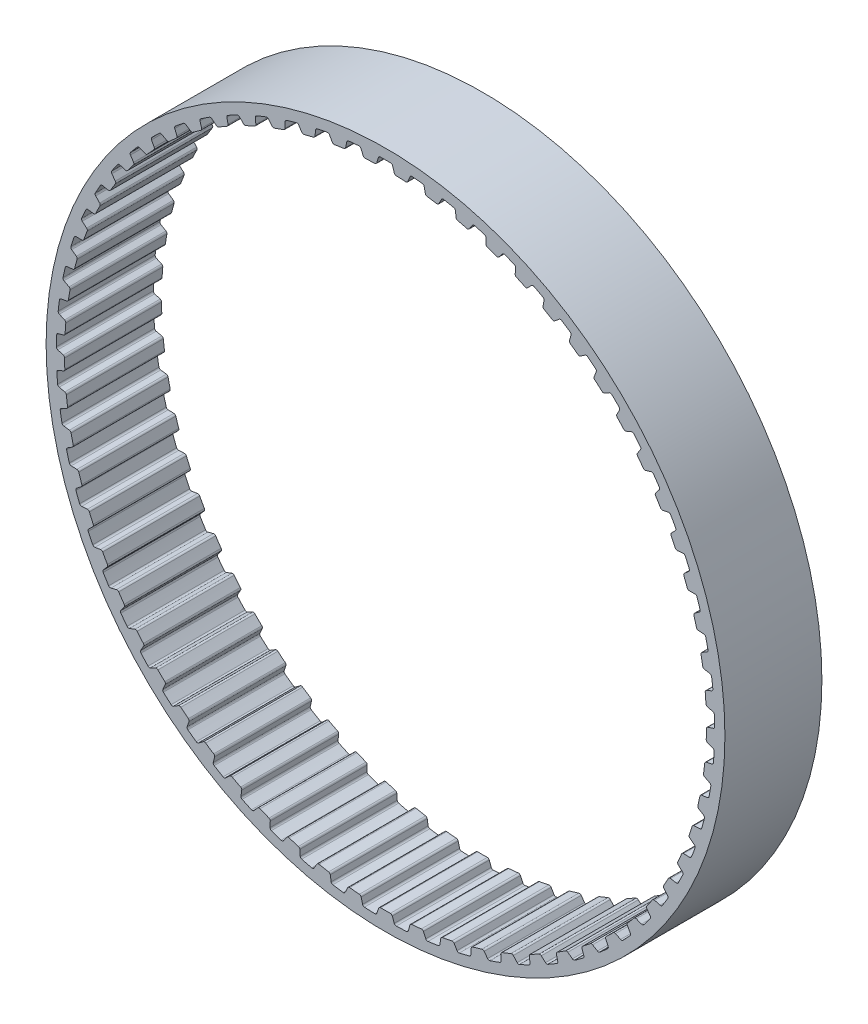
SolidWorks part; units mm, degrees
ref_plane "Front Plane" through (0, 0, 0) normal (0, 0, 1) x (1, 0, 0)
ref_plane "Top Plane" through (0, 0, 0) normal (0, 1, 0) x (1, 0, 0)
ref_plane "Right Plane" through (0, 0, 0) normal (1, 0, 0) x (0, 0, -1)
sketch "Sketch1" plane through (0, 0, 0) normal (0, 0, 1) x (1, 0, 0)
  line L0 (0, 0) -> (-0.9594, 19.8343) construction
  line L1 (0, 0) -> (0.9594, 19.8343) construction
  line L2 (0.9594, 19.8343) -> (-0.9594, 19.8343) construction
  line L3 (0.9594, 19.8343) -> (-0.9594, 19.8343) construction
  circle A0 centre (0, 0) radius 21.0005
  circle A1 centre (0, 0) radius 19.8575
  circle A2 centre (0, 0) radius 20.3655 construction
  dimension "OD" = 42.001
  dimension "Angle Distance" = 5.538
  dimension "hs" = 1.143
  dimension "ht" = 0.508
sketch "Sketch4" plane through (0, 0, 0) normal (0, 0, 1) x (1, 0, 0)
  circle A0 centre (0, 0) radius 19.8575 construction
  circle A1 centre (0, 0) radius 21.0005 construction
  circle A2 centre (0, 0) radius 19.8575
  circle A3 centre (0, 0) radius 21.0005
extrude "Boss-Extrude1" add sketch "Sketch4" along normal mid plane 6
sketch "Sketch2" plane through (0, 0, 0) normal (0, 0, 1) x (1, 0, 0)
  line L1 (0, 21.0005) -> (0, 0) construction
  line L2 (-1.015, 20.1073) -> (1.015, 20.1073) construction
  line L4 (-0.5696, 19.8532) -> (-1.3491, 19.8155)
  line L5 (-0.5696, 19.8532) -> (-0.412, 20.3613)
  line L6 (-1.3491, 19.8155) -> (-1.555, 20.3061)
  line L7 (0, 0) -> (-0.9594, 19.8343) construction
  line L8 (-0.412, 20.3613) -> (-1.555, 20.3061) construction
  line L9 (0.412, 20.3613) -> (1.555, 20.3061) construction
  line L10 (1.3491, 19.8155) -> (1.555, 20.3061)
  line L11 (0.5696, 19.8532) -> (0.412, 20.3613)
  line L12 (0.5696, 19.8532) -> (1.3491, 19.8155)
  line L13 (0, 0) -> (8.0365, 19.4019) construction
  line L14 (-1.015, 20.1073) -> (-3.0347, 19.9028) construction
  line L15 (-2.0248, 20.005) -> (0, 0) construction
  line L16 (-3.0347, 19.9028) -> (-2.9932, 19.6306) construction
  circle A0 centre (0, 0) radius 20.3655 construction
  circle A1 centre (0, 0) radius 20.3655
  circle A2 centre (0, 0) radius 20.1073 construction
  circle A4 centre (0, 0) radius 21.0005 construction
  circle A5 centre (0, 0) radius 19.8575 construction
  point P16 (-0.4908, 20.1073)
  point P20 (0, 20.1073)
  dimension "D1" = 22.5
  dimension "bt" = 1.143
  dimension "b" = 40
  dimension "Pitch" = 2.03
sketch "Sketch3" plane through (0, 0, 0) normal (0, 0, 1) x (1, 0, 0)
  line L0 (-0.6611, 19.8465) -> (0.6611, 19.8465)
  line L2 (-0.5696, 19.8532) -> (-0.412, 20.3613) construction
  line L3 (0.5696, 19.8532) -> (0.412, 20.3613) construction
  line L5 (-0.544, 19.9358) -> (-0.4392, 20.2736)
  line L7 (0.544, 19.9358) -> (0.4392, 20.2736)
  arc A0 (0.544, 19.9358) -> (0.6611, 19.8465) centre (0.6653, 19.9734) ccw
  circle A1 centre (0, 0) radius 20.3655 construction
  arc A2 (0.3199, 20.363) -> (-0.3199, 20.363) centre (0, 0) ccw
  arc A3 (-0.544, 19.9358) -> (-0.6611, 19.8465) centre (-0.6653, 19.9734) cw
  arc A4 (0.4392, 20.2736) -> (0.3199, 20.363) centre (0.3179, 20.236) ccw
  arc A5 (-0.4392, 20.2736) -> (-0.3199, 20.363) centre (-0.3179, 20.236) cw
  circle A6 centre (0, 0) radius 19.8575 construction
  arc A7 (-0.6611, 19.8465) -> (0.6611, 19.8465) centre (0, 0) ccw construction
  dimension "ra" = 0.127
  dimension "rr" = 0.127
extrude "Cut-Extrude1" cut sketch "Sketch3" against normal mid plane 6
pattern_circular "CirPattern1" count 65 over 360 about axis through (0, 0, 0) along (0, 0, 1) of "Cut-Extrude1"
equation "\"D1@Cut-Extrude1\" = \"Width@Boss-Extrude1\""
